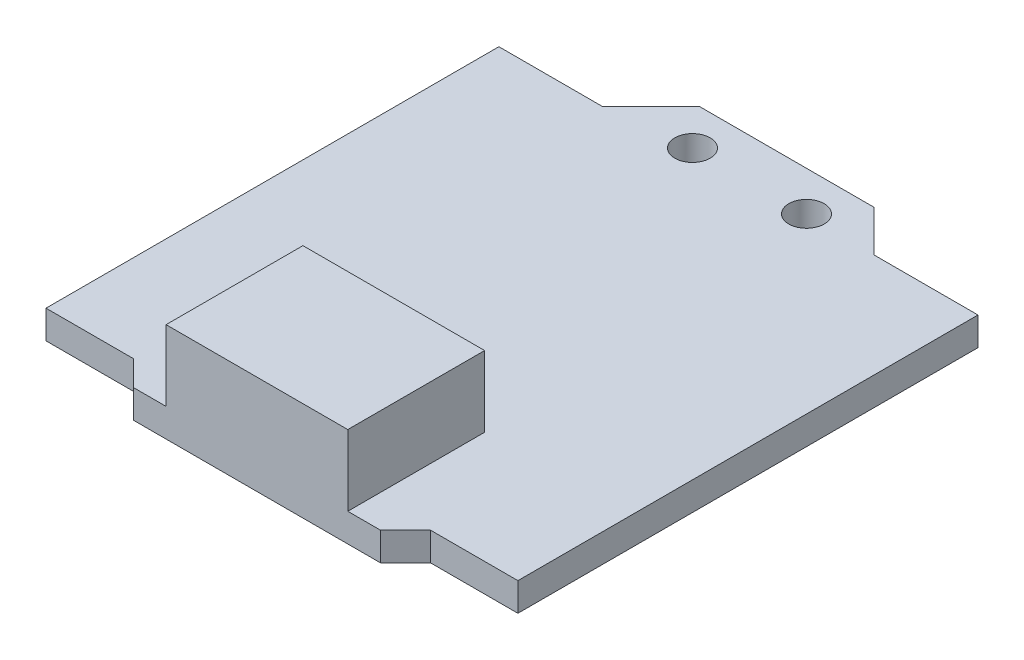
SolidWorks part; units mm, degrees
ref_plane "Front Plane" through (0, 0, 0) normal (0, 0, 1) x (1, 0, 0)
ref_plane "Top Plane" through (0, 0, 0) normal (0, 1, 0) x (1, 0, 0)
ref_plane "Right Plane" through (0, 0, 0) normal (1, 0, 0) x (0, 0, -1)
sketch "Sketch1" plane through (0, 0, 0) normal (0, 1, 0) x (1, 0, 0)
  line L0 (-13.0313, -6.6565) -> (-13.0313, 12.5374)
  line L1 (-13.0313, 12.5374) -> (-8.6313, 12.5374)
  line L2 (-8.6313, 12.5374) -> (-6.5752, 14.5935)
  line L3 (-6.5752, 14.5935) -> (0.8187, 14.5935)
  line L4 (0.8187, 14.5935) -> (2.5687, 12.8435)
  line L5 (2.5687, 12.8435) -> (6.9687, 12.8435)
  line L6 (6.9687, 12.8435) -> (6.9687, -6.6565)
  line L7 (6.9687, -6.6565) -> (3.2687, -6.6565)
  line L8 (3.2687, -6.6565) -> (2.208, -7.7172)
  line L9 (2.208, -7.7172) -> (-8.2706, -7.7172)
  line L10 (-8.2706, -7.7172) -> (-9.3313, -6.6565)
  line L11 (-9.3313, -6.6565) -> (-13.0313, -6.6565)
  point P9 (0, 0)
  dimension "D1" = 20
  dimension "D2" = 19.5
  dimension "D3" = 4.4
  dimension "D4" = 4.4
  dimension "D5" = 3.7
  dimension "D6" = 3.7
  dimension "D7" = 2.0561
  dimension "D8" = 135
  dimension "D9" = 1.5
  dimension "D10" = 1.75
extrude "Boss-Extrude1" add sketch "Sketch1" along normal blind 1.2
sketch "Sketch2" plane through (0, 1.2, 0) normal (0, 1, 0) x (1, 0, 0)
  line L0 (-8.2706, -7.7172) -> (2.208, -7.7172) construction
  line L1 (-6.8813, -1.9172) -> (0.8187, -1.9172)
  line L2 (-6.8813, -1.9172) -> (-6.8813, -7.7172)
  line L3 (-6.8813, -7.7172) -> (0.8187, -7.7172)
  line L4 (0.8187, -1.9172) -> (0.8187, -7.7172)
  line L5 (6.9687, -6.6565) -> (6.9687, 12.8435) construction
  dimension "D1" = 5.8
  dimension "D2" = 7.7
  dimension "D3" = 0
  dimension "D4" = 6.15
extrude "Boss-Extrude2" add sketch "Sketch2" along normal blind 3
sketch "Sketch5" plane through (0, 1.2, 0) normal (0, 1, 0) x (1, 0, 0)
  circle A0 centre (-5.2097, 12.9207) radius 0.75
  circle A1 centre (-0.3775, 12.9207) radius 0.75
  point P4 (-0.2442, 12.9207)
  point P5 (-5.2097, 12.9207)
  point P6 (-0.3775, 12.9207)
  dimension "D1" = 1.5
  dimension "D2" = 1.5
extrude "Cut-Extrude1" cut sketch "Sketch5" against normal blind 3
